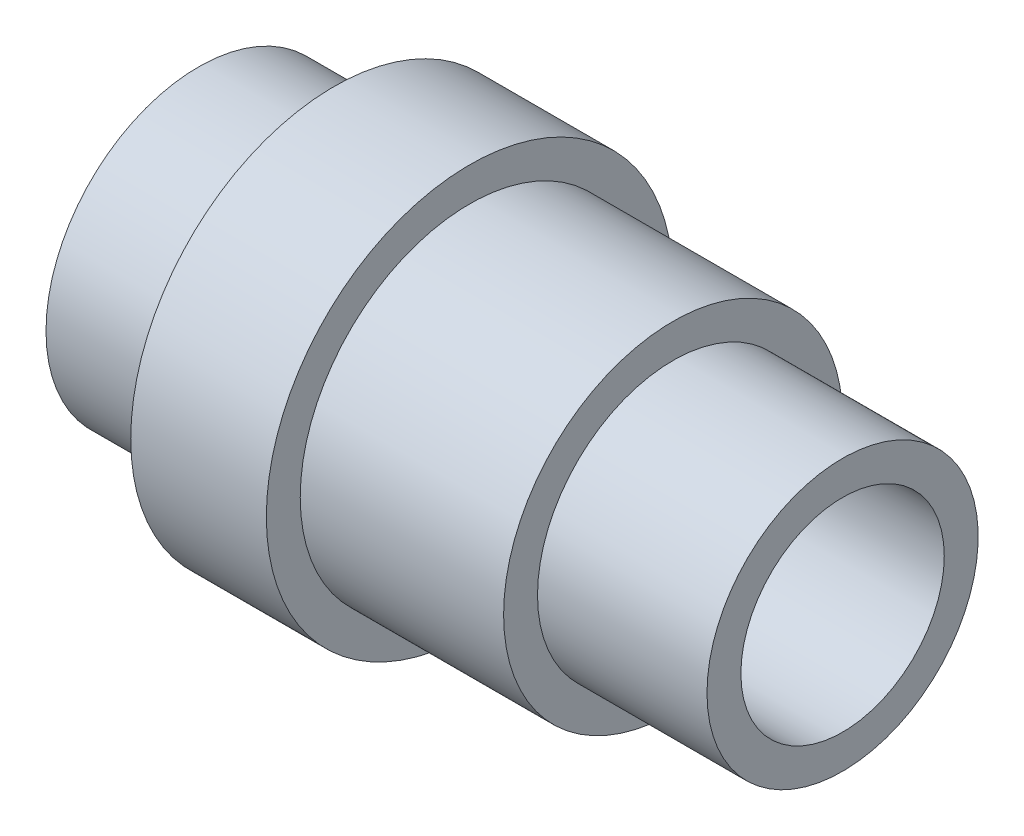
SolidWorks part; units mm, degrees
ref_plane "Front Plane" through (0, 0, 0) normal (0, 0, 1) x (1, 0, 0)
ref_plane "Top Plane" through (0, 0, 0) normal (0, 1, 0) x (1, 0, 0)
ref_plane "Right Plane" through (0, 0, 0) normal (1, 0, 0) x (0, 0, -1)
sketch "Sketch1" plane through (0, 0, 0) normal (0, 0, 1) x (1, 0, 0)
  line L0 (-25.9539, 0) -> (32.6625, 0) construction
  line L1 (-47.5, 22.5) -> (-47.5, 15)
  line L2 (-47.5, 15) -> (47.5, 15)
  line L3 (47.5, 15) -> (47.5, 20)
  line L4 (47.5, 20) -> (22.5, 20)
  line L5 (22.5, 20) -> (22.5, 25)
  line L6 (22.5, 25) -> (-7.5, 25)
  line L7 (-7.5, 25) -> (-7.5, 30)
  line L8 (-7.5, 30) -> (-27.5, 30)
  line L9 (-27.5, 30) -> (-27.5, 22.5)
  line L10 (-27.5, 22.5) -> (-47.5, 22.5)
  line L11 (0, -14.4036) -> (0, 17.5804) construction
  point P3 (0, 15)
  dimension "D1" = 20
  dimension "D2" = 25
  dimension "D3" = 55
  dimension "D4" = 95
  dimension "D5" = 5
  dimension "D6" = 5
  dimension "D7" = 5
  dimension "D8" = 7.5
  dimension "D9" = 15
revolve "Revolve1" add sketch "Sketch1" angle 360 about L0
